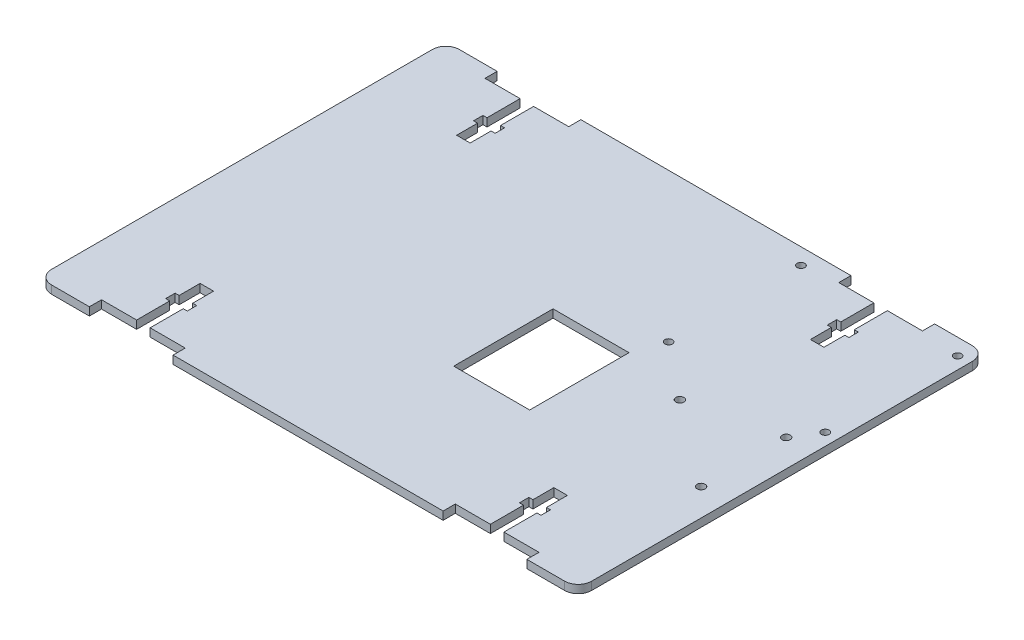
SolidWorks part; units mm, degrees
ref_plane "Front Plane" through (0, 0, 0) normal (0, 0, 1) x (1, 0, 0)
ref_plane "Top Plane" through (0, 0, 0) normal (0, 1, 0) x (1, 0, 0)
ref_plane "Right Plane" through (0, 0, 0) normal (1, 0, 0) x (0, 0, -1)
sketch "Sketch1" plane through (0, 0, 0) normal (0, 1, 0) x (1, 0, 0)
  line L1 (-100, -75.5) -> (100, -75.5)
  line L2 (-100, -75.5) -> (-100, 75.5)
  line L3 (-100, 75.5) -> (100, 75.5)
  line L4 (100, -75.5) -> (100, 75.5)
  line L5 (-100, -75.5) -> (100, 75.5) construction
  line L6 (-100, 75.5) -> (100, -75.5) construction
  point P0 (0, 0)
extrude "Boss-Extrude1" add sketch "Sketch1" along normal blind 3
ref_plane "Plane1" through (0, 3, 0) normal (0, 1, 0) x (1, 0, 0)
sketch "Sketch2" plane through (0, 3, 0) normal (0, 1, 0) x (1, 0, 0)
  line L0 (100, 75.5) -> (-100, 75.5) construction
  line L1 (-100, 75.5) -> (-68, 75.5) construction
  line L2 (-100, 75.5) -> (-100, 47.5) construction
  line L3 (-100, 47.5) -> (-68, 47.5) construction
  line L4 (-68, 75.5) -> (-68, 47.5) construction
  line L5 (-100, 75.5) -> (-100, -75.5) construction
  line L6 (-65.5, 47.5) -> (-65.5, 57) construction
  line L7 (-68, 75.5) -> (-63, 75.5) construction
  line L8 (-68, 75.5) -> (-68, 47.5) construction
  line L9 (-68, 47.5) -> (-63, 47.5) construction
  line L10 (-63, 75.5) -> (-63, 47.5) construction
  line L11 (-68, 75.5) -> (-63, 75.5)
  line L12 (-69.5, 55.25) -> (-61.5, 55.25) construction
  line L13 (-69.5, 55.25) -> (-69.5, 58.75) construction
  line L14 (-69.5, 58.75) -> (-61.5, 58.75) construction
  line L15 (-61.5, 55.25) -> (-61.5, 58.75) construction
  line L16 (-69.5, 55.25) -> (-61.5, 58.75) construction
  line L17 (-69.5, 58.75) -> (-61.5, 55.25) construction
  line L18 (-81, 71) -> (-68, 71)
  line L19 (-63, 58.75) -> (-61.5, 58.75)
  line L20 (-61.5, 58.75) -> (-61.5, 55.25)
  line L21 (-61.5, 55.25) -> (-63, 55.25)
  line L22 (-63, 55.25) -> (-63, 47.5)
  line L23 (-63, 47.5) -> (-68, 47.5)
  line L24 (-68, 47.5) -> (-68, 55.25)
  line L25 (-68, 55.25) -> (-69.5, 55.25)
  line L26 (-69.5, 55.25) -> (-69.5, 58.75)
  line L27 (-69.5, 58.75) -> (-68, 58.75)
  line L28 (-68, 71) -> (-68, 58.75)
  line L29 (-65.5, 75.5) -> (-50, 75.5) construction
  line L30 (-81, 75.5) -> (-50, 75.5) construction
  line L31 (-50, 71) -> (-63, 71)
  line L32 (-81, 75.5) -> (-50, 75.5)
  line L33 (-81, 75.5) -> (-81, 71)
  line L34 (-81, 71) -> (-50, 71) construction
  line L35 (-50, 75.5) -> (-50, 71)
  line L36 (-63, 71) -> (-63, 58.75)
  line L37 (-63, 58.75) -> (-62.9809, 58.8083)
  line L38 (0, -75.5) -> (0, 75.5) construction
  line L39 (-100, 0) -> (100, 0) construction
  line L40 (81, 71) -> (50, 71) construction
  line L41 (81, 75.5) -> (50, 75.5) construction
  line L42 (65.5, 75.5) -> (50, 75.5) construction
  line L43 (69.5, 58.75) -> (61.5, 55.25) construction
  line L44 (69.5, 55.25) -> (61.5, 58.75) construction
  line L45 (61.5, 55.25) -> (61.5, 58.75) construction
  line L46 (69.5, 58.75) -> (61.5, 58.75) construction
  line L47 (69.5, 55.25) -> (69.5, 58.75) construction
  line L48 (69.5, 55.25) -> (61.5, 55.25) construction
  line L49 (63, 75.5) -> (63, 47.5) construction
  line L50 (68, 47.5) -> (63, 47.5) construction
  line L51 (68, 75.5) -> (68, 47.5) construction
  line L52 (68, 75.5) -> (63, 75.5) construction
  line L53 (65.5, 47.5) -> (65.5, 57) construction
  line L54 (68, 75.5) -> (68, 47.5) construction
  line L56 (100, 75.5) -> (100, 47.5) construction
  line L57 (100, 75.5) -> (68, 75.5) construction
  line L58 (63, 58.75) -> (62.9809, 58.8083)
  line L59 (63, 71) -> (63, 58.75)
  line L60 (50, 75.5) -> (50, 71)
  line L61 (81, 75.5) -> (81, 71)
  line L62 (81, 75.5) -> (50, 75.5)
  line L63 (50, 71) -> (63, 71)
  line L64 (68, 71) -> (68, 58.75)
  line L65 (69.5, 58.75) -> (68, 58.75)
  line L66 (69.5, 55.25) -> (69.5, 58.75)
  line L67 (68, 55.25) -> (69.5, 55.25)
  line L68 (68, 47.5) -> (68, 55.25)
  line L69 (63, 47.5) -> (68, 47.5)
  line L70 (63, 55.25) -> (63, 47.5)
  line L71 (61.5, 55.25) -> (63, 55.25)
  line L72 (61.5, 58.75) -> (61.5, 55.25)
  line L73 (63, 58.75) -> (61.5, 58.75)
  line L74 (81, 71) -> (68, 71)
  line L75 (68, 75.5) -> (63, 75.5)
  line L76 (100, -75.5) -> (100, 75.5) construction
  line L77 (100, -75.5) -> (68, -75.5) construction
  line L78 (100, -75.5) -> (100, -47.5) construction
  line L79 (100, -47.5) -> (68, -47.5) construction
  line L80 (68, -75.5) -> (68, -47.5) construction
  line L81 (65.5, -47.5) -> (65.5, -57) construction
  line L82 (68, -75.5) -> (63, -75.5) construction
  line L83 (68, -75.5) -> (68, -47.5) construction
  line L84 (68, -47.5) -> (63, -47.5) construction
  line L85 (63, -75.5) -> (63, -47.5) construction
  line L86 (69.5, -55.25) -> (61.5, -55.25) construction
  line L87 (69.5, -55.25) -> (69.5, -58.75) construction
  line L88 (69.5, -58.75) -> (61.5, -58.75) construction
  line L89 (61.5, -55.25) -> (61.5, -58.75) construction
  line L90 (69.5, -55.25) -> (61.5, -58.75) construction
  line L91 (69.5, -58.75) -> (61.5, -55.25) construction
  line L92 (65.5, -75.5) -> (50, -75.5) construction
  line L93 (81, -75.5) -> (50, -75.5) construction
  line L94 (81, -71) -> (50, -71) construction
  line L95 (-81, -71) -> (-50, -71) construction
  line L96 (-81, -75.5) -> (-50, -75.5) construction
  line L97 (-65.5, -75.5) -> (-50, -75.5) construction
  line L98 (-69.5, -58.75) -> (-61.5, -55.25) construction
  line L99 (-69.5, -55.25) -> (-61.5, -58.75) construction
  line L100 (-61.5, -55.25) -> (-61.5, -58.75) construction
  line L101 (-69.5, -58.75) -> (-61.5, -58.75) construction
  line L102 (-69.5, -55.25) -> (-69.5, -58.75) construction
  line L103 (-69.5, -55.25) -> (-61.5, -55.25) construction
  line L104 (-63, -75.5) -> (-63, -47.5) construction
  line L105 (-68, -47.5) -> (-63, -47.5) construction
  line L106 (-68, -75.5) -> (-68, -47.5) construction
  line L107 (-68, -75.5) -> (-63, -75.5) construction
  line L108 (-65.5, -47.5) -> (-65.5, -57) construction
  line L109 (-68, -75.5) -> (-68, -47.5) construction
  line L110 (-100, -47.5) -> (-68, -47.5) construction
  line L111 (-100, -75.5) -> (-100, -47.5) construction
  line L112 (-100, -75.5) -> (-68, -75.5) construction
  line L113 (68, -75.5) -> (63, -75.5)
  line L114 (81, -71) -> (68, -71)
  line L115 (63, -58.75) -> (61.5, -58.75)
  line L116 (61.5, -58.75) -> (61.5, -55.25)
  line L117 (61.5, -55.25) -> (63, -55.25)
  line L118 (63, -55.25) -> (63, -47.5)
  line L119 (63, -47.5) -> (68, -47.5)
  line L120 (68, -47.5) -> (68, -55.25)
  line L121 (68, -55.25) -> (69.5, -55.25)
  line L122 (69.5, -55.25) -> (69.5, -58.75)
  line L123 (69.5, -58.75) -> (68, -58.75)
  line L124 (68, -71) -> (68, -58.75)
  line L125 (50, -71) -> (63, -71)
  line L126 (81, -75.5) -> (50, -75.5)
  line L127 (81, -75.5) -> (81, -71)
  line L128 (50, -75.5) -> (50, -71)
  line L129 (63, -71) -> (63, -58.75)
  line L130 (63, -58.75) -> (62.9809, -58.8083)
  line L131 (-63, -58.75) -> (-62.9809, -58.8083)
  line L132 (-63, -71) -> (-63, -58.75)
  line L133 (-50, -75.5) -> (-50, -71)
  line L134 (-81, -75.5) -> (-81, -71)
  line L135 (-81, -75.5) -> (-50, -75.5)
  line L136 (-50, -71) -> (-63, -71)
  line L137 (-68, -71) -> (-68, -58.75)
  line L138 (-69.5, -58.75) -> (-68, -58.75)
  line L139 (-69.5, -55.25) -> (-69.5, -58.75)
  line L140 (-68, -55.25) -> (-69.5, -55.25)
  line L141 (-68, -47.5) -> (-68, -55.25)
  line L142 (-63, -47.5) -> (-68, -47.5)
  line L143 (-63, -55.25) -> (-63, -47.5)
  line L144 (-61.5, -55.25) -> (-63, -55.25)
  line L145 (-61.5, -58.75) -> (-61.5, -55.25)
  line L146 (-63, -58.75) -> (-61.5, -58.75)
  line L147 (-81, -71) -> (-68, -71)
  line L148 (-68, -75.5) -> (-63, -75.5)
  line L149 (100, 0) -> (24, 0) construction
  line L150 (24, 75.5) -> (24, 0.5) construction
  line L151 (24, -75.5) -> (24, -10.5) construction
  line L152 (-100, -75.5) -> (100, -75.5) construction
  line L153 (24, 0.5) -> (15, 0.5) construction
  line L154 (19.5, -10.5) -> (19.5, -16) construction
  line L155 (15, 0.5) -> (24, 0.5) construction
  line L156 (15, 0.5) -> (15, -10.5) construction
  line L157 (15, -10.5) -> (24, -10.5) construction
  line L158 (24, 0.5) -> (24, -10.5) construction
  line L159 (19.5, -16) -> (6.75, -16) construction
  line L160 (-100, 75.5) -> (-89.3934, 64.8934) construction
  line L161 (6.75, -16) -> (32, -16) construction
  line L162 (6.75, -16) -> (6.75, 8.5) construction
  line L163 (6.75, 8.5) -> (32, 8.5) construction
  line L164 (32, -16) -> (32, 8.5) construction
  line L165 (-89.3934, 64.8934) -> (-89.3934, -5.1066) construction
  line L166 (89.92, -19.9) -> (89.92, 11.61) construction
  line L167 (-89.3934, -5.1066) -> (-29.3934, -5.1066) construction
  line L168 (-89.3934, -5.1066) -> (-89.3934, 64.8934) construction
  line L169 (-89.3934, 64.8934) -> (-29.3934, 64.8934) construction
  line L170 (-29.3934, -5.1066) -> (-29.3934, 64.8934) construction
  line L171 (100, -75.5) -> (89.92, -75.5) construction
  line L172 (100, -75.5) -> (100, -19.9) construction
  line L173 (100, -19.9) -> (89.92, -19.9) construction
  line L174 (89.92, -75.5) -> (89.92, -19.9) construction
  line L175 (89.92, -6.4831) -> (58.16, -6.4831)
  line L176 (58.16, -75.5) -> (58.16, 4) construction
  line L177 (95.5, 69.5) -> (95.5, 20.5) construction
  line L178 (6.75, -16) -> (32, -16) construction
  line L179 (6.75, -16) -> (6.75, -32.0716) construction
  line L180 (6.75, -32.0716) -> (32, -32.0716) construction
  line L181 (32, -16) -> (32, -32.0716) construction
  line L182 (5.5077, 9.6842) -> (33.6375, 9.6842)
  line L183 (5.5077, 9.6842) -> (5.5077, -27.0879)
  line L184 (5.5077, -27.0879) -> (33.6375, -27.0879)
  line L185 (33.6375, 9.6842) -> (33.6375, -27.0879)
  line L186 (100, 75.5) -> (95.5, 75.5) construction
  line L187 (100, 75.5) -> (100, 65.5) construction
  line L189 (95.5, 75.5) -> (95.5, 69.5) construction
  line L191 (95.5, 20.5) -> (37.5, 20.5) construction
  line L192 (95.5, 20.5) -> (95.5, 69.5) construction
  line L193 (95.5, 69.5) -> (37.5, 69.5) construction
  line L194 (37.5, 20.5) -> (37.5, 69.5) construction
  circle A4 centre (89.92, -19.9) radius 1.5
  circle A5 centre (89.92, 11.61) radius 1.5
  circle A6 centre (58.16, 4) radius 1.5
  circle A7 centre (95.5, 20.5) radius 1.4
  circle A8 centre (37.5, 20.5) radius 1.4
  circle A9 centre (37.5, 69.5) radius 1.4
  circle A10 centre (95.5, 69.5) radius 1.4
  point P25 (-65.5, 75.5)
  point P78 (0, 0)
extrude "Cut-Extrude2" cut sketch "Sketch2" against normal through all
fillet "Fillet1" radius 5 4 edges at (100, 1.5, -75.5) (100, 1.5, 75.5) (-100, 1.5, 75.5) (-100, 1.5, -75.5)
